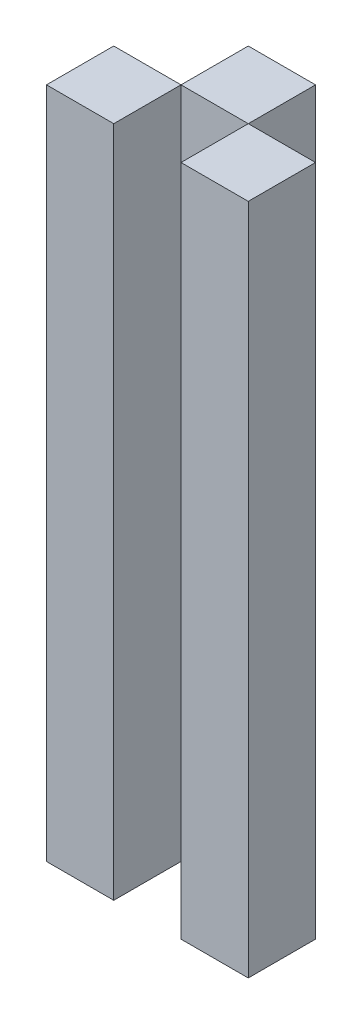
SolidWorks part; units mm, degrees
ref_plane "Front Plane" through (0, 0, 0) normal (0, 0, 1) x (1, 0, 0)
ref_plane "Top Plane" through (0, 0, 0) normal (0, 1, 0) x (1, 0, 0)
ref_plane "Right Plane" through (0, 0, 0) normal (1, 0, 0) x (0, 0, -1)
ref_plane "Plane4"
sketch "Sketch1" plane through (0, 0, 0) normal (0, 0, 1) x (1, 0, 0)
  line L0 (76.2, 254) -> (50.8047, 254)
  line L1 (50.8047, 254) -> (50.8047, 0)
  line L2 (50.8047, 0) -> (76.2, 0)
  line L3 (76.2, 0) -> (76.2, 254)
  line L4 (0, 0) -> (25.4047, 0)
  line L5 (25.4047, 0) -> (25.4047, 254)
  line L6 (25.4047, 254) -> (0, 254)
  line L7 (0, 254) -> (0, 0)
  dimension "D1" = 76.2
  dimension "D2" = 254
  dimension "D3" = 25.4
  dimension "D4" = 254
extrude "Extrusion2" add sketch "Sketch1" along normal blind 25.4 contours L2 L3 L0 L1 | L6 L7 L4 L5
sketch "Sketch2" plane through (0, 0, 0) normal (0, 0, -1) x (-1, 0, 0)
  line L0 (-25.4047, 0) -> (-50.8047, 0)
  line L1 (-50.8047, 0) -> (-50.8047, 254)
  line L2 (-50.8047, 254) -> (-25.4047, 254)
  line L3 (-25.4047, 254) -> (-25.4047, 0)
  dimension "D1" = 76.2
  dimension "D2" = 254
  dimension "D3" = 25.4
  dimension "D4" = 254
extrude "Extrusion3" add sketch "Sketch2" along normal blind 25.4
